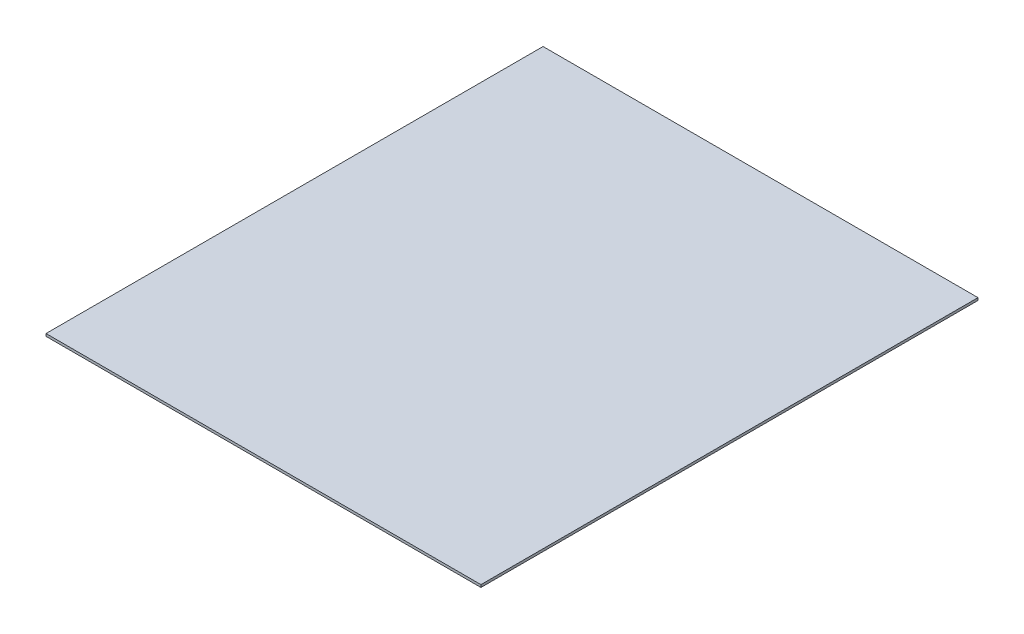
SolidWorks part; units mm, degrees
ref_plane "前视基准面" through (0, 0, 0) normal (0, 0, 1) x (1, 0, 0)
ref_plane "上视基准面" through (0, 0, 0) normal (0, 1, 0) x (1, 0, 0)
ref_plane "右视基准面" through (0, 0, 0) normal (1, 0, 0) x (0, 0, -1)
sketch "草图1" plane through (0, 0, 0) normal (1, 0, 0) x (0, 0, -1)
  line L0 (-200, 0) -> (200, 0)
  line L1 (-200, -2) -> (200, -2)
  line L2 (200, 0) -> (200, -2)
  line L3 (-200, 0) -> (-200, -2)
  dimension "D1" = 400
  dimension "D2" = 2
  dimension "D4" = 200
extrude "凸台-拉伸1" add sketch "草图1" along normal mid plane 350
